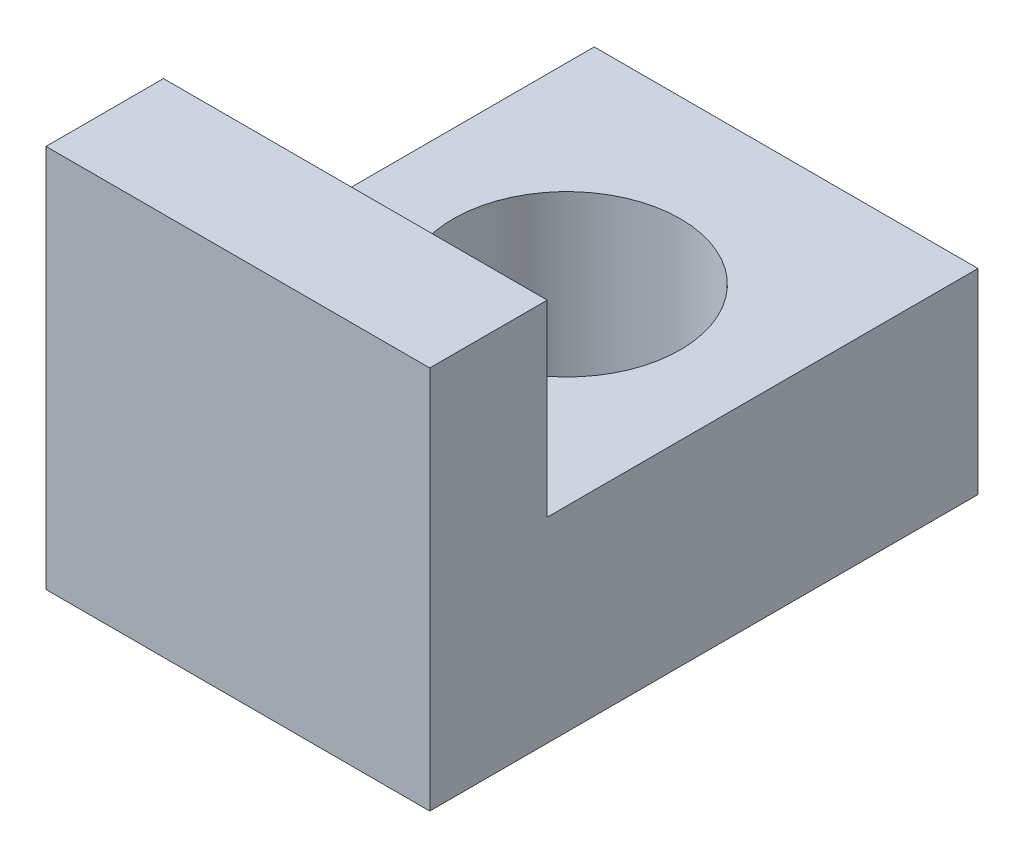
SolidWorks part; units mm, degrees
ref_plane "Front Plane" through (0, 0, 0) normal (0, 0, 1) x (1, 0, 0)
ref_plane "Top Plane" through (0, 0, 0) normal (0, 1, 0) x (1, 0, 0)
ref_plane "Right Plane" through (0, 0, 0) normal (1, 0, 0) x (0, 0, -1)
sketch "Sketch1" plane through (0, 0, 0) normal (1, 0, 0) x (0, 0, -1)
  line L0 (0, 0) -> (0, 4.9)
  line L1 (0, 4.9) -> (1.5, 4.9)
  line L2 (1.5, 4.9) -> (1.5, 2.5)
  line L3 (1.5, 2.5) -> (7, 2.5)
  line L4 (7, 2.5) -> (7, 0)
  line L5 (7, 0) -> (0, 0)
  dimension "D1" = 4.9
  dimension "D2" = 2.5
  dimension "D3" = 7
  dimension "D4" = 1.5
extrude "Boss-Extrude1" add sketch "Sketch1" along normal blind 4.9
sketch "Sketch2" plane through (0, 0, 0) normal (0, -1, 0) x (1, 0, 0)
  line L0 (2.45, 0) -> (2.45, -8.4721) construction
  line L1 (4.9, 0) -> (0, 0) construction
  circle A0 centre (2.45, -4.2) radius 1.45
  dimension "D1" = 2.9
  dimension "D2" = 4.2
extrude "Cut-Extrude1" cut sketch "Sketch2" against normal through all
